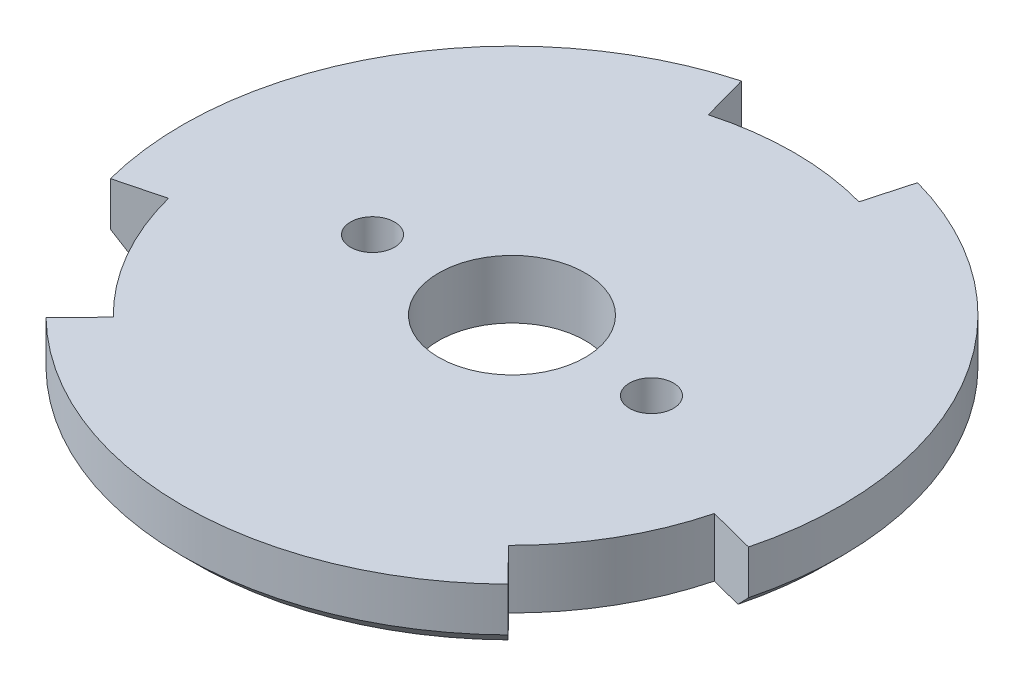
SolidWorks part; units mm, degrees
ref_plane "Front Plane" through (0, 0, 0) normal (0, 0, 1) x (1, 0, 0)
ref_plane "Top Plane" through (0, 0, 0) normal (0, 1, 0) x (1, 0, 0)
ref_plane "Right Plane" through (0, 0, 0) normal (1, 0, 0) x (0, 0, -1)
sketch "Sketch1" plane through (0, 0, 0) normal (0, 1, 0) x (1, 0, 0)
  line L0 (0, 0) -> (0, 26.8494) construction
  circle A0 centre (0, 0) radius 22.5
  circle A1 centre (0, 0) radius 5
  circle A2 centre (-9.525, 0) radius 1.5
  circle A3 centre (9.525, 0) radius 1.5
  point P7 (0, 0)
  point P8 (0, 0)
  dimension "D1" = 45
  dimension "D2" = 10
  dimension "D3" = 3
  dimension "D4" = 19.05
extrude "Boss-Extrude1" add sketch "Sketch1" along normal blind 4
chamfer "Chamfer1" distance 1 angle 45 1 edges at (0, 0, 22.5)
sketch "Sketch2" plane through (0, 4, 0) normal (0, 1, 0) x (1, 0, 0)
  line L0 (0, 0) -> (0, 22.5) construction
  line L1 (6.0129, 21.6817) -> (5.1443, 18.5499)
  line L2 (-6.0129, 21.6817) -> (-5.1443, 18.5499)
  line L3 (21.7833, -5.6336) -> (18.6368, -4.8198)
  line L4 (15.7705, -16.0481) -> (13.4925, -13.7301)
  line L5 (-15.7705, -16.0481) -> (-13.4925, -13.7301)
  line L6 (-21.7833, -5.6336) -> (-18.6368, -4.8198)
  arc A0 (6.0129, 21.6817) -> (-6.0129, 21.6817) centre (0, 0) ccw
  circle A1 centre (0, 0) radius 22.5 construction
  arc A2 (5.1443, 18.5499) -> (-5.1443, 18.5499) centre (0, 0) ccw
  arc A3 (15.7705, -16.0481) -> (21.7833, -5.6336) centre (0, 0) ccw
  arc A4 (13.4925, -13.7301) -> (18.6368, -4.8198) centre (0, 0) ccw
  arc A5 (-21.7833, -5.6336) -> (-15.7705, -16.0481) centre (0, 0) ccw
  arc A6 (-18.6368, -4.8198) -> (-13.4925, -13.7301) centre (0, 0) ccw
  point P20 (0, 0)
  dimension "D1" = 19.25
  dimension "D2" = 15.5
  dimension "D3" = 3
extrude "Cut-Extrude1" cut sketch "Sketch2" against normal through all
